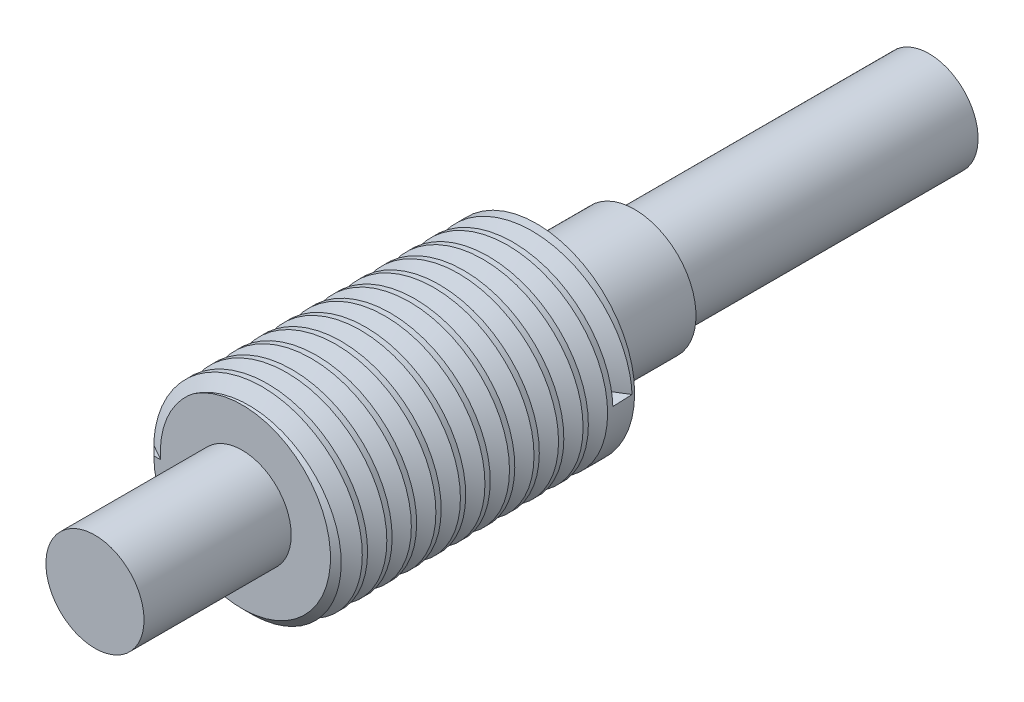
SolidWorks part; units mm, degrees
ref_plane "Front Plane" through (0, 0, 0) normal (0, 0, 1) x (1, 0, 0)
ref_plane "Top Plane" through (0, 0, 0) normal (0, 1, 0) x (1, 0, 0)
ref_plane "Right Plane" through (0, 0, 0) normal (1, 0, 0) x (0, 0, -1)
sketch "Sketch1" plane through (0, 0, 0) normal (0, 0, 1) x (1, 0, 0)
  circle A0 centre (0, 0) radius 1
  dimension "D1" = 2
extrude "Boss-Extrude1" add sketch "Sketch1" along normal blind 3
chamfer "Chamfer1" distance 0.1 angle 45 1 edges at (1, 0, 3)
sketch "Sketch3" plane through (0, 0, 3) normal (0, 0, 1) x (1, 0, 0)
  circle A0 centre (0, 0) radius 1 construction
  circle A1 centre (0, 0) radius 1
curve "Helix/Spiral1" pitch 0.25 height 2.875 turns 11.5
ref_plane "Plane1" through (-1, 0, 3) normal (0, 0.9992, -0.0398) x (1, 0, 0)
sketch "Sketch4" plane through (-1, 0, 3) normal (0, 0.9992, -0.0398) x (1, 0, 0)
  line L1 (0.1697, 0.0006) -> (-0.0209, 0.1106)
  line L2 (-0.0209, 0.1106) -> (-0.0209, -0.1094)
  line L3 (-0.0209, -0.1094) -> (0.1697, 0.0006)
  circle A0 centre (0.0427, 0.0006) radius 0.0635 construction
  point P1 (0.0427, 0.0006)
  dimension "D1" = 0.22
sweep "Cut-Sweep1" cut profiles "Sketch4" path "Helix/Spiral1"
sketch "Sketch5" plane through (0, 0, 0) normal (0, 0, -1) x (-1, 0, 0)
  circle A0 centre (0, 0) radius 0.625
  dimension "D1" = 1.25
extrude "Boss-Extrude2" add sketch "Sketch5" along normal blind 1
sketch "Sketch6" plane through (0, 0, -1) normal (0, 0, -1) x (-1, 0, 0)
  circle A0 centre (0, 0) radius 0.5
  dimension "D1" = 1
extrude "Boss-Extrude3" add sketch "Sketch6" along normal blind 3
sketch "Sketch7" plane through (0, 0, 3) normal (0, 0, 1) x (1, 0, 0)
  circle A0 centre (0, 0) radius 0.5
  dimension "D1" = 1
extrude "Boss-Extrude4" add sketch "Sketch7" along normal blind 1.5
